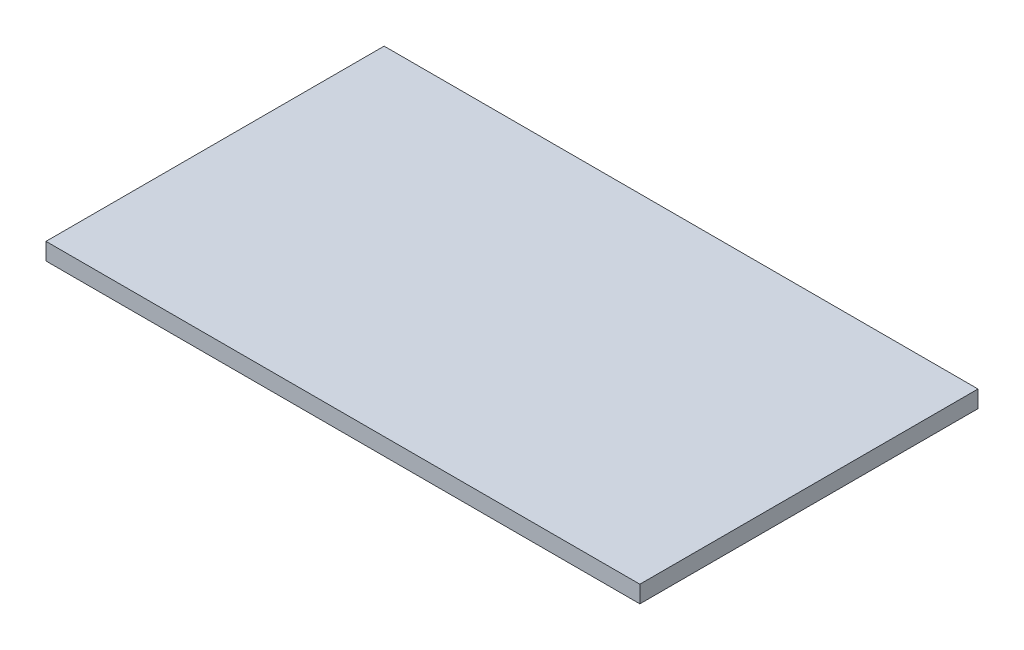
SolidWorks part; units mm, degrees
ref_plane "Спереди" through (0, 0, 0) normal (0, 0, 1) x (1, 0, 0)
ref_plane "Сверху" through (0, 0, 0) normal (0, 1, 0) x (1, 0, 0)
ref_plane "Справа" through (0, 0, 0) normal (1, 0, 0) x (0, 0, -1)
sketch "Эскиз1" plane through (0, 0, 0) normal (0, 1, 0) x (1, 0, 0)
  line L1 (313.5, -178.5) -> (-313.5, -178.5)
  line L2 (313.5, -178.5) -> (313.5, 178.5)
  line L3 (313.5, 178.5) -> (-313.5, 178.5)
  line L4 (-313.5, -178.5) -> (-313.5, 178.5)
  line L5 (313.5, -178.5) -> (-313.5, 178.5) construction
  line L6 (313.5, 178.5) -> (-313.5, -178.5) construction
  point P0 (0, 0)
  dimension "D1" = 627
  dimension "D2" = 357
extrude "Бобышка-Вытянуть1" add sketch "Эскиз1" along normal blind 18
